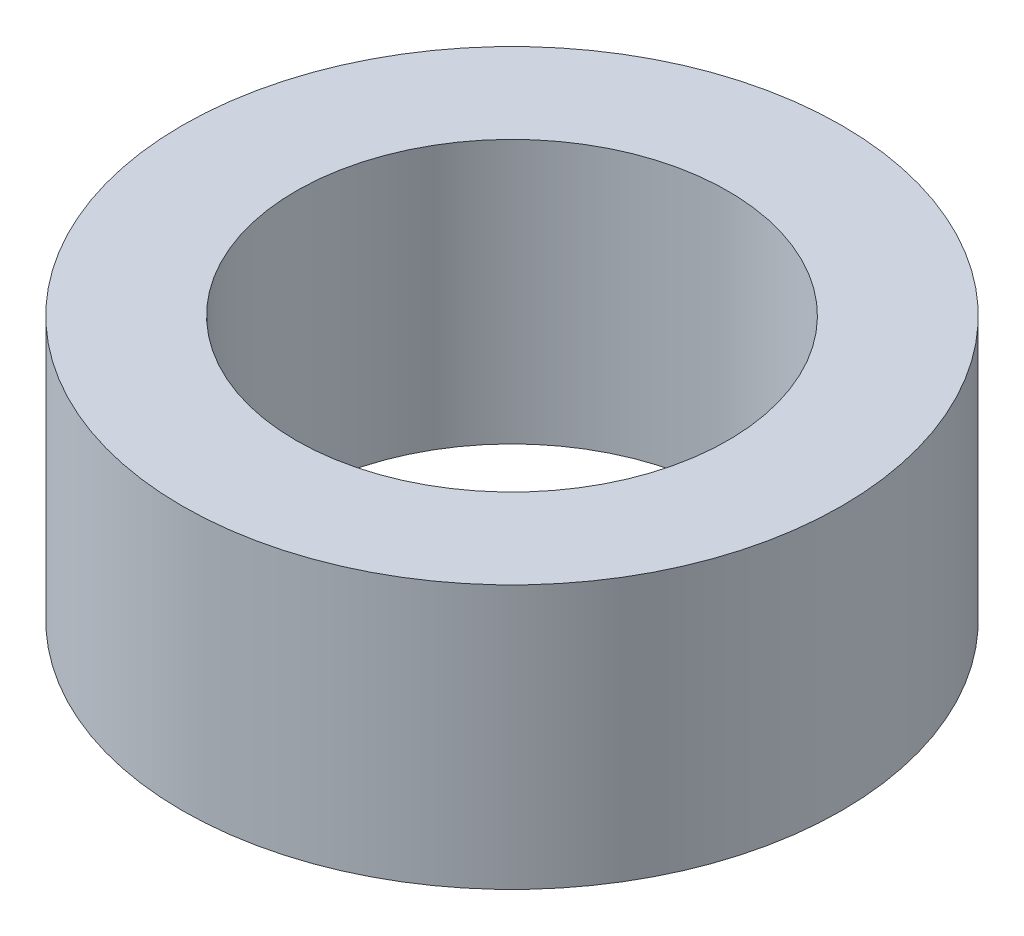
SolidWorks part; units mm, degrees
material "Nylon 6/10"
ref_plane "Front Plane" through (0, 0, 0) normal (0, 0, 1) x (1, 0, 0)
ref_plane "Top Plane" through (0, 0, 0) normal (0, 1, 0) x (1, 0, 0)
ref_plane "Right Plane" through (0, 0, 0) normal (1, 0, 0) x (0, 0, -1)
sketch "Sketch1" plane through (0, 0, 0) normal (0, 1, 0) x (1, 0, 0)
  circle A0 centre (0, 0) radius 3.9688
  circle A1 centre (0, 0) radius 2.6
  dimension "D1" = 5.2
  dimension "D2" = 7.9375
extrude "Boss-Extrude1" add sketch "Sketch1" along normal blind 3.175
